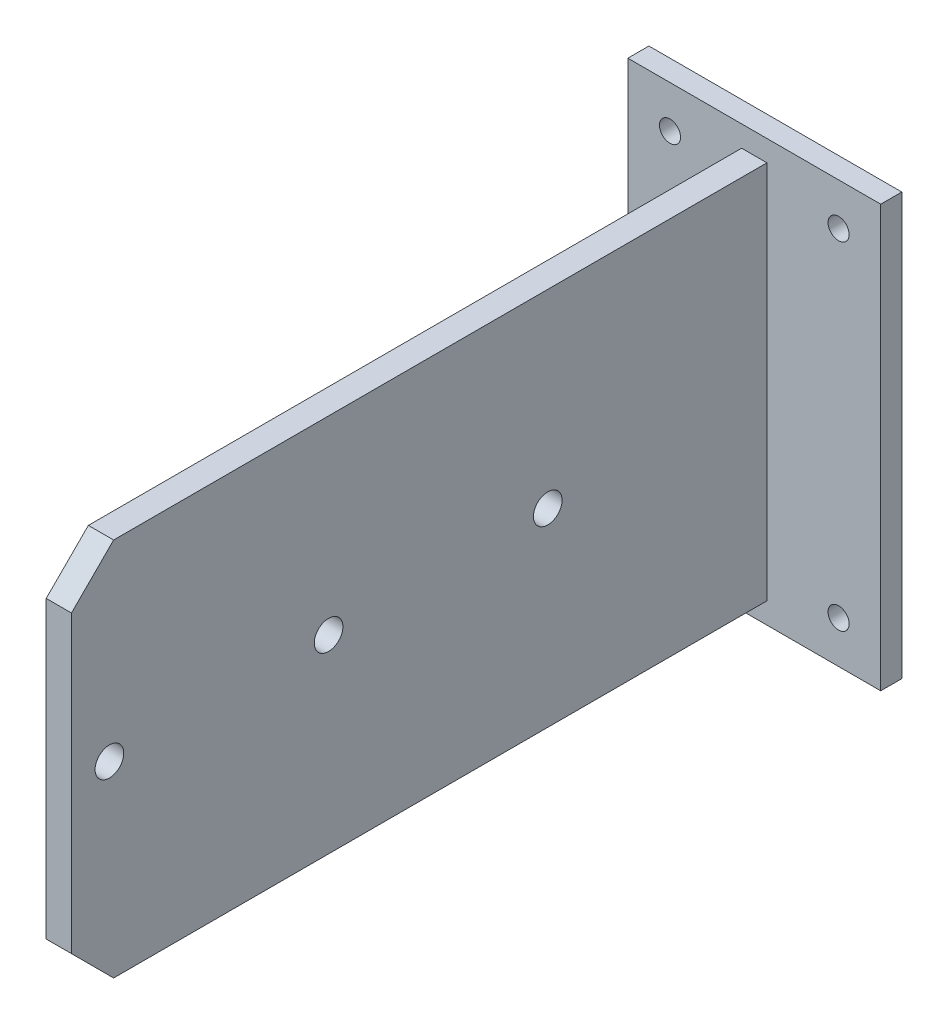
SolidWorks part; units mm, degrees
ref_plane "Front Plane" through (0, 0, 0) normal (0, 0, 1) x (1, 0, 0)
ref_plane "Top Plane" through (0, 0, 0) normal (0, 1, 0) x (1, 0, 0)
ref_plane "Right Plane" through (0, 0, 0) normal (1, 0, 0) x (0, 0, -1)
sketch "Sketch1" plane through (0, 0, 0) normal (0, 0, 1) x (1, 0, 0)
  line L0 (0, 0) -> (0, 50) construction
  line L1 (-30, -50) -> (30, -50)
  line L2 (-30, -50) -> (-30, 50)
  line L3 (-30, 50) -> (30, 50)
  line L4 (30, -50) -> (30, 50)
  line L5 (-30, -50) -> (30, 50) construction
  line L6 (-30, 50) -> (30, -50) construction
  line L7 (0, 0) -> (-30, 0) construction
  circle A0 centre (-20, 40) radius 2.5
  circle A1 centre (20, 40) radius 2.5
  circle A2 centre (20, -40) radius 2.5
  circle A3 centre (-20, -40) radius 2.5
  point P0 (0, 0)
  dimension "D3" = 5
  dimension "D1" = 100
  dimension "D2" = 60
  dimension "D4" = 40
  dimension "D5" = 80
extrude "Boss-Extrude1" add sketch "Sketch1" along normal blind 5
sketch "Sketch2" plane through (0, 0, 5) normal (0, 0, 1) x (1, 0, 0)
  line L0 (0, 50) -> (0, -50) construction
  line L2 (-3, -45) -> (3, -45)
  line L3 (-3, -45) -> (-3, 45)
  line L4 (30, -50) -> (30, 50)
  line L5 (30, 50) -> (-30, 50)
  line L6 (-30, 50) -> (-30, -50)
  line L7 (-30, -50) -> (30, -50)
  line L8 (30, -50) -> (30, 50)
  line L9 (30, 50) -> (-30, 50)
  line L10 (-30, 50) -> (-30, -50)
  line L11 (-30, -50) -> (30, -50)
  line L12 (-3, 45) -> (3, 45)
  line L13 (3, -45) -> (3, 45)
  line L14 (-3, -45) -> (3, 45) construction
  line L15 (-3, 45) -> (3, -45) construction
  point P6 (0, 0)
  dimension "D2" = 6
  dimension "D3" = 90
  dimension "D1" = 0
extrude "Boss-Extrude2" add sketch "Sketch2" along normal blind 165 contours L2 L13 L12 L3
chamfer "Chamfer1" distance 10 angle 45 2 edges at (0, -45, 170) (0, 45, 170)
sketch "Sketch3" plane through (-3, 0, 0) normal (-1, 0, 0) x (0, 0, 1)
  line L0 (170, 0) -> (0, 0) construction
  line L6 (5, -45) -> (160, -45)
  line L7 (160, -45) -> (170, -35)
  line L8 (170, -35) -> (170, 35)
  line L9 (170, 35) -> (160, 45)
  line L10 (160, 45) -> (5, 45)
  line L11 (5, 45) -> (5, -45)
  line L12 (5, -45) -> (160, -45)
  line L13 (160, -45) -> (170, -35)
  line L14 (170, -35) -> (170, 35)
  line L15 (170, 35) -> (160, 45)
  line L16 (160, 45) -> (5, 45)
  line L17 (5, 45) -> (5, -45)
  circle A0 centre (161, 0) radius 3.4
  circle A1 centre (109, 0) radius 3.4
  circle A2 centre (57, 0) radius 3.4
  point P15 (64.2584, 0)
  point P16 (160.684, 0)
  dimension "D2" = 6.8
  dimension "D3" = 52
  dimension "D4" = 52
  dimension "D5" = 9
  dimension "D1" = 0
extrude "Cut-Extrude1" cut sketch "Sketch3" against normal blind 165 contours L0 A2 | A2 L0 | L0 A1 | A1 L0 | L0 A0 | A0 L0
